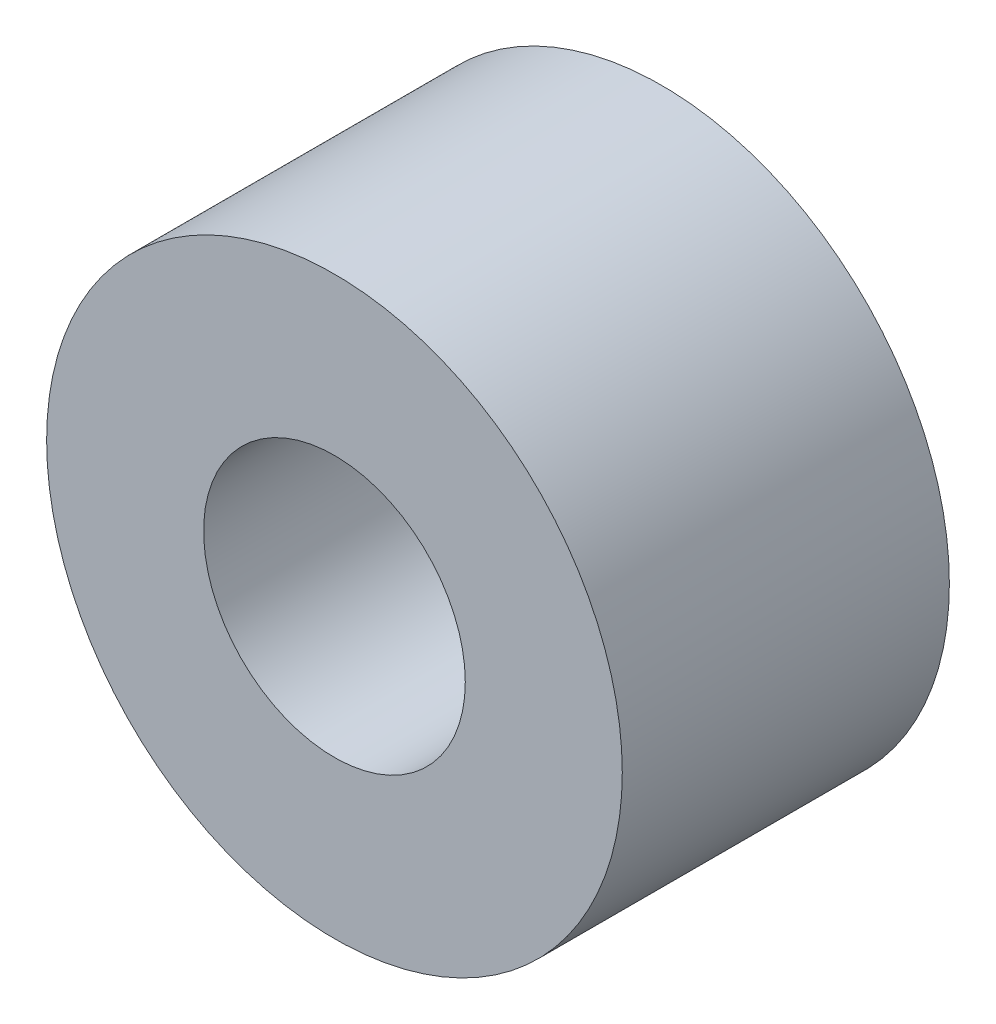
SolidWorks part; units mm, degrees
ref_plane "Front Plane" through (0, 0, 0) normal (0, 0, 1) x (1, 0, 0)
ref_plane "Top Plane" through (0, 0, 0) normal (0, 1, 0) x (1, 0, 0)
ref_plane "Right Plane" through (0, 0, 0) normal (1, 0, 0) x (0, 0, -1)
sketch "Sketch1" plane through (0, 0, 0) normal (0, 0, 1) x (1, 0, 0)
  circle A0 centre (0, 0) radius 1.6
  circle A1 centre (0, 0) radius 3.52
  dimension "D1" = 3.2
  dimension "D2" = 1.92
extrude "Boss-Extrude1" add sketch "Sketch1" along normal blind 4
